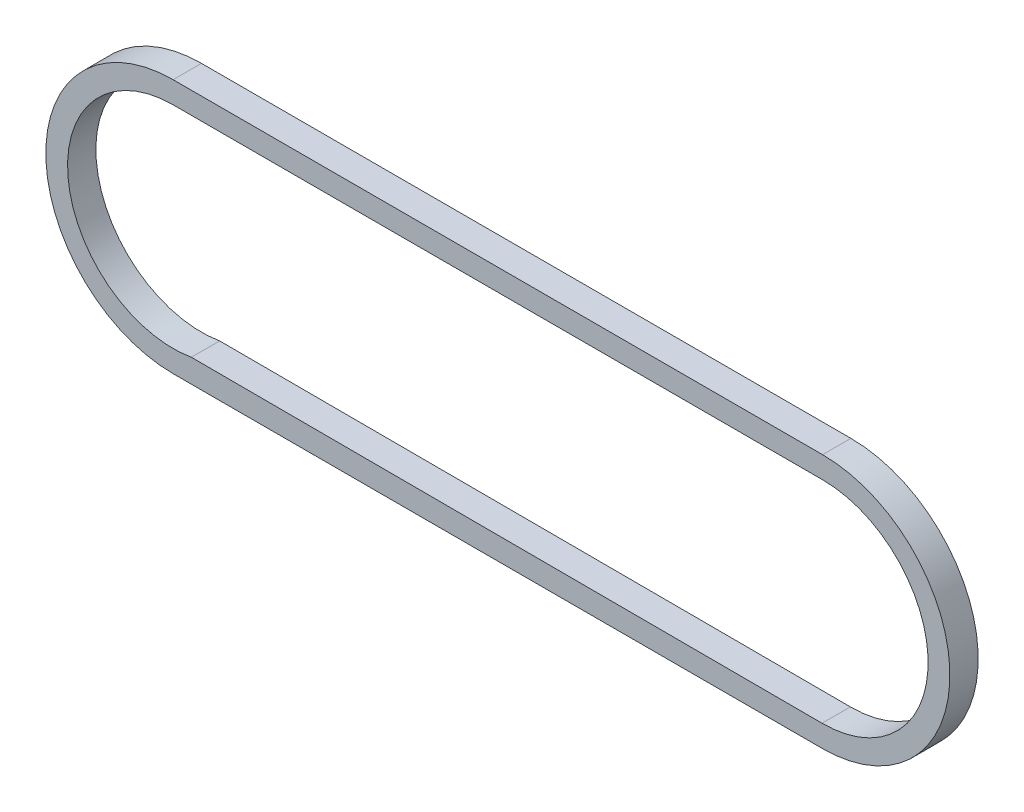
SolidWorks part; units mm, degrees
material "1.0037 (S235JR)"
ref_plane "Płaszczyzna przednia" through (0, 0, 0) normal (0, 0, 1) x (1, 0, 0)
ref_plane "Płaszczyzna górna" through (0, 0, 0) normal (0, 1, 0) x (1, 0, 0)
ref_plane "Płaszczyzna prawa" through (0, 0, 0) normal (1, 0, 0) x (0, 0, -1)
sketch "Szkic1" plane through (0, 0, 0) normal (0, 0, 1) x (1, 0, 0)
  line L0 (0, -49) -> (-250, -49)
  line L1 (-250, 49) -> (0, 49)
  line L2 (0, -40.63) -> (-250, -40)
  line L3 (-250, 40.63) -> (0, 40.63)
  arc A0 (-0.2048, -40.6295) -> (0, 40.63) centre (0, 0) ccw
  arc A1 (0, -49) -> (0, 49) centre (0, 0) ccw
  arc A2 (-250, 40.63) -> (-242.9729, -40.0177) centre (-250, 0) ccw
  arc A3 (-250, 49) -> (-250, -49) centre (-250, 0) ccw
  dimension "D1" = 98
  dimension "D2" = 81.26
  dimension "D3" = 81.26
  dimension "D4" = 98
extrude "Dodanie-wyciągnięcie1" add sketch "Szkic1" along normal blind 1 and the other way blind 9.9 contours L1 A3 L0 A1 A2 L3 A0 L2
